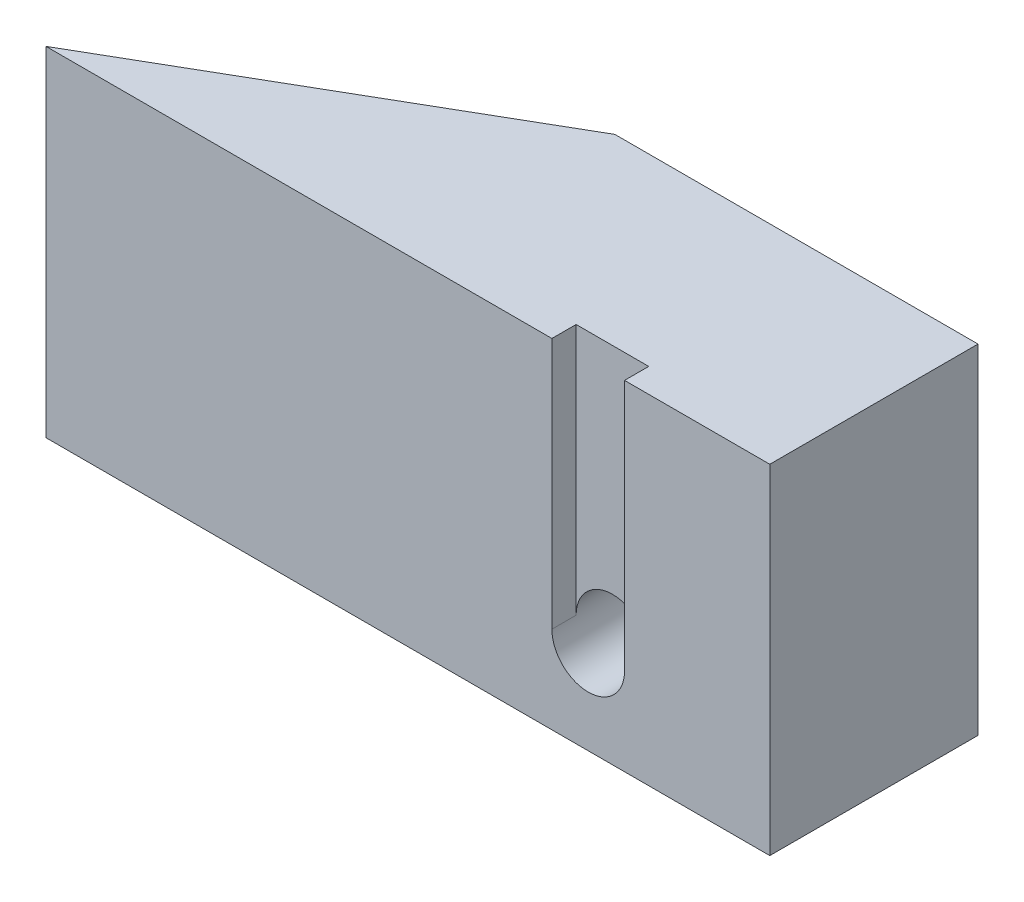
SolidWorks part; units mm, degrees
ref_plane "Front Plane" through (0, 0, 0) normal (0, 0, 1) x (1, 0, 0)
ref_plane "Top Plane" through (0, 0, 0) normal (0, 1, 0) x (1, 0, 0)
ref_plane "Right Plane" through (0, 0, 0) normal (1, 0, 0) x (0, 0, -1)
sketch "Sketch1" plane through (0, 0, 0) normal (0, 1, 0) x (1, 0, 0)
  line L0 (-111.9782, 0) -> (37.5, 0)
  line L9 (0, 0) -> (0, 43) construction
  line L10 (-37.5, 43) -> (37.5, 43)
  line L11 (-111.9782, 0) -> (-37.5, 43)
  line L13 (37.5, 43) -> (37.5, 0)
  point P3 (0, 0)
  point P12 (0, 43)
  dimension "D1" = 75
  dimension "D3" = 43
  dimension "D4" = 30
extrude "Boss-Extrude1" add sketch "Sketch1" along normal blind 70
sketch "Sketch3" plane through (0, 0, 0) normal (0, 0, 1) x (1, 0, 0)
  line L1 (-111.9782, 0) -> (37.5, 0) construction
  circle A0 centre (0, 18) radius 3
  dimension "D1" = 6
  dimension "D2" = 18
extrude "Cut-Extrude1" cut sketch "Sketch3" against normal through all
sketch "Sketch7" plane through (0, 0, 0) normal (0, 0, 1) x (1, 0, 0)
  circle A0 centre (0, 18) radius 7.5
  dimension "D1" = 15
extrude "Cut-Extrude3" cut sketch "Sketch7" against normal blind 30 and the other way through all
sketch "Sketch5" plane through (0, 0, 0) normal (0, 0, 1) x (1, 0, 0)
  line L0 (0, 18) -> (0, 70) construction
  line L3 (-7.5, 70) -> (7.5, 70)
  line L4 (-7.5, 70) -> (-7.5, 18)
  line L5 (-7.5, 18) -> (7.5, 18)
  line L6 (7.5, 70) -> (7.5, 18)
  line L7 (-7.5, 70) -> (7.5, 18) construction
  line L8 (-7.5, 18) -> (7.5, 70) construction
  point P5 (0, 44)
  dimension "D1" = 15
extrude "Cut-Extrude2" cut sketch "Sketch5" against normal blind 5
fillet "Fillet1" [suppressed] radius 1
